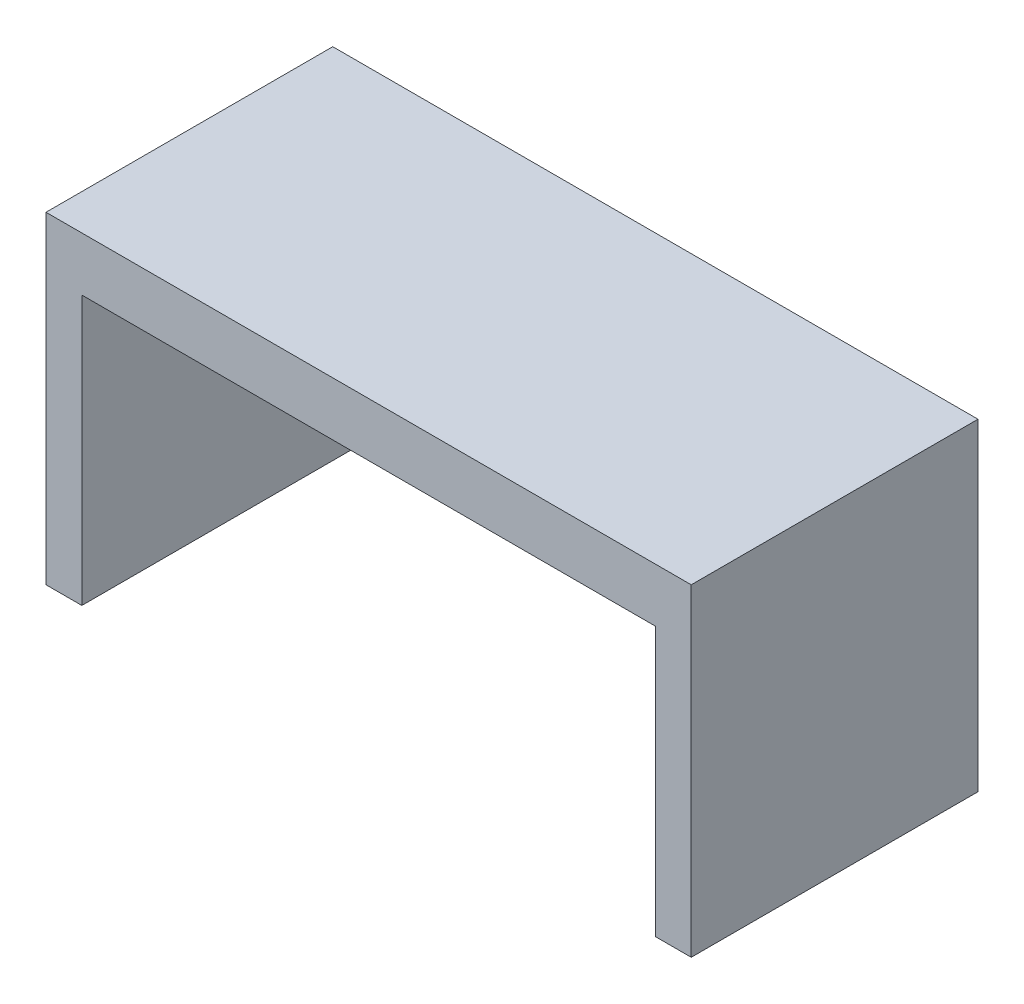
SolidWorks part; units mm, degrees
ref_plane "Front Plane" through (0, 0, 0) normal (0, 0, 1) x (1, 0, 0)
ref_plane "Top Plane" through (0, 0, 0) normal (0, 1, 0) x (1, 0, 0)
ref_plane "Right Plane" through (0, 0, 0) normal (1, 0, 0) x (0, 0, -1)
sketch "Sketch1" plane through (0, 0, 0) normal (0, 1, 0) x (1, 0, 0)
  line L1 (-903.0612, 272.449) -> (896.9388, 272.449)
  line L2 (-903.0612, 272.449) -> (-903.0612, -527.551)
  line L3 (-903.0612, -527.551) -> (896.9388, -527.551)
  line L4 (896.9388, 272.449) -> (896.9388, -527.551)
  dimension "D1" = 1800
  dimension "D2" = 800
extrude "Boss-Extrude1" add sketch "Sketch1" along normal blind 900
sketch "Sketch2" plane through (0, 0, 527.551) normal (0, 0, 1) x (1, 0, 0)
  line L0 (-903.0612, 0) -> (896.9388, 0) construction
  line L1 (-803.0612, 750) -> (796.9388, 750)
  line L2 (-803.0612, 750) -> (-803.0612, 0)
  line L3 (-803.0612, 0) -> (796.9388, 0)
  line L4 (796.9388, 750) -> (796.9388, 0)
  line L5 (-903.0612, 900) -> (896.9388, 900) construction
  line L6 (-903.0612, 900) -> (-903.0612, 0) construction
  line L7 (896.9388, 900) -> (896.9388, 0) construction
  dimension "D1" = 0
  dimension "D2" = 150
  dimension "D3" = 100
  dimension "D4" = 100
extrude "Cut-Extrude1" cut sketch "Sketch2" against normal blind 1200
sketch "Sketch3" plane through (0, 750, 0) normal (0, -1, 0) x (1, 0, 0)
  line L0 (796.9388, 527.551) -> (-803.0612, 527.551) construction
  line L1 (796.9388, -272.449) -> (796.9388, 527.551) construction
  circle A0 centre (-3.0612, 77.551) radius 22.2365
  dimension "D1" = 450
  dimension "D2" = 800
extrude "Boss-Extrude2" add sketch "Sketch3" along normal blind 20 separate body
